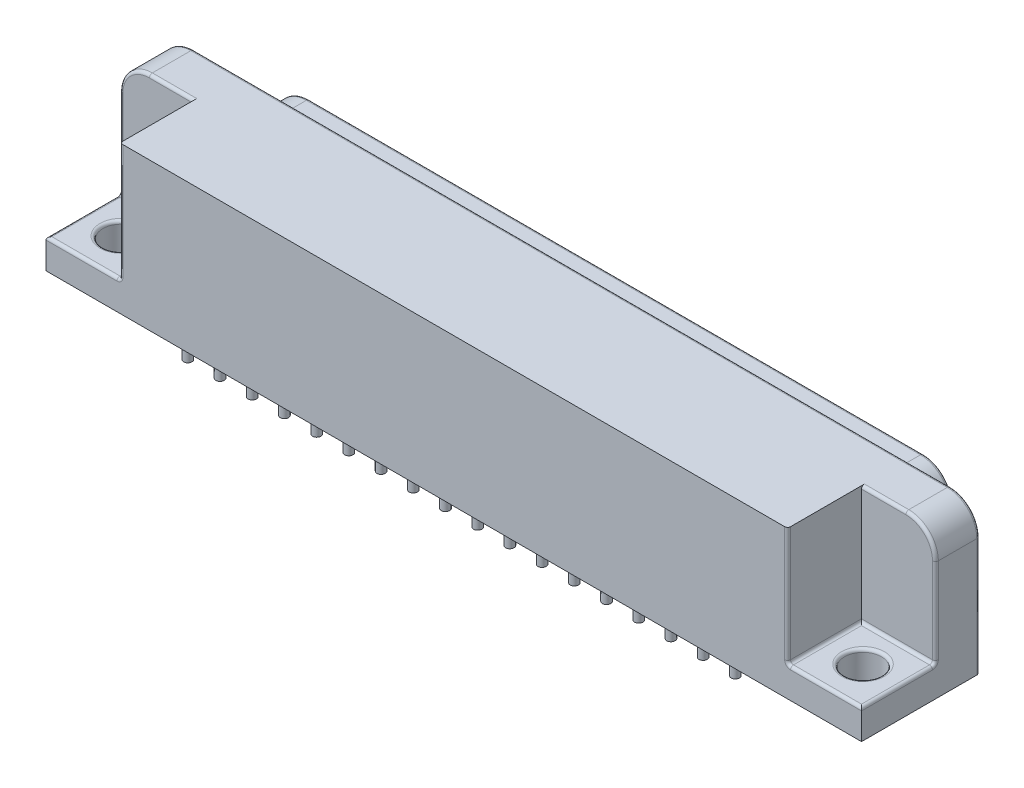
SolidWorks part; units mm, degrees
ref_plane "Front Plane" through (0, 0, 0) normal (0, 0, 1) x (1, 0, 0)
ref_plane "Top Plane" through (0, 0, 0) normal (0, 1, 0) x (1, 0, 0)
ref_plane "Right Plane" through (0, 0, 0) normal (1, 0, 0) x (0, 0, -1)
sketch "Sketch1" plane through (0, 0, 0) normal (0, 1, 0) x (1, 0, 0)
  line L1 (-10.16, -2.032) -> (59.944, -2.032)
  line L2 (-10.16, -2.032) -> (-10.16, 8.128)
  line L3 (-10.16, 8.128) -> (59.944, 8.128)
  line L4 (59.944, -2.032) -> (59.944, 8.128)
  point P3 (24.892, 8.128)
  dimension "D1" = 70.104
  dimension "D2" = 10.16
  dimension "D3" = 2.032
  dimension "D4" = 10.16
extrude "Base-Extrude" add sketch "Sketch1" along normal blind 12.7
sketch "Sketch2" plane through (0, 0, -8.128) normal (0, 0, -1) x (-1, 0, 0)
  line L0 (-24.892, 12.7) -> (-24.892, -6.5379) construction
  line L1 (-59.944, 12.7) -> (10.16, 12.7) construction
  line L2 (-50.7446, 2.286) -> (0.9606, 2.286)
  line L3 (3.4543, 4.3435) -> (3.9949, 7.1375)
  line L4 (1.5011, 10.16) -> (-51.2851, 10.16)
  line L6 (-53.2383, 4.3435) -> (-53.7789, 7.1375)
  line L7 (-59.944, 0) -> (10.16, 0) construction
  arc A0 (3.4543, 4.3435) -> (0.9606, 2.286) centre (0.9606, 4.826) cw
  arc A1 (1.5011, 10.16) -> (3.9949, 7.1375) centre (1.5011, 7.62) cw
  arc A2 (-51.2851, 10.16) -> (-53.7789, 7.1375) centre (-51.2851, 7.62) ccw
  arc A3 (-53.2383, 4.3435) -> (-50.7446, 2.286) centre (-50.7446, 4.826) ccw
  point P4 (-24.892, 10.16)
  point P12 (3.0563, 2.286)
  point P21 (-24.892, 2.286)
  dimension "D5" = 2.54
  dimension "D1" = 2.286
  dimension "D2" = 2.54
  dimension "D3" = 100.95
  dimension "D4" = 27.9483
extrude "Boss-Extrude1" add sketch "Sketch2" along normal blind 3.81
sketch "Sketch4" plane through (0, 0, -11.938) normal (0, 0, -1) x (-1, 0, 0)
  line L0 (10.16, 12.7) -> (10.16, 0) construction
  line L2 (-59.944, 12.7) -> (10.16, 12.7) construction
  circle A0 centre (0, 7.62) radius 0.635
  dimension "D1" = 1.27
  dimension "D2" = 10.16
  dimension "D3" = 5.08
extrude "Cut-Extrude1" cut sketch "Sketch4" against normal blind 5.08
sketch "Sketch5" plane through (0, 0, -11.938) normal (0, 0, -1) x (-1, 0, 0)
  line L0 (10.16, 12.7) -> (10.16, 0) construction
  line L2 (-59.944, 0) -> (10.16, 0) construction
  circle A0 centre (-1.397, 5.08) radius 0.635
  circle A1 centre (0, 7.62) radius 0.635 construction
  dimension "D2" = 5.08
  dimension "D1" = 11.557
extrude "Cut-Extrude2" cut sketch "Sketch5" against normal blind 5.08
sketch "Sketch6" plane through (0, 0, 0) normal (0, -1, 0) x (1, 0, 0)
  circle A0 centre (0, 0) radius 0.3556
  dimension "D1" = 0.7112
extrude "Boss-Extrude2" add sketch "Sketch6" along normal blind 2.54
pattern_linear "LPattern1" count 19 spacing 2.7686 along (1, 0, 0) skipping (18, 0) of "Boss-Extrude2"
pattern_linear "LPattern2" count 19 spacing 2.7686 along (1, 0, 0) of "Cut-Extrude1"
pattern_linear "LPattern3" count 18 spacing 2.7686 along (1, 0, 0) of "Cut-Extrude2"
sketch "Sketch7" plane through (0, 0, 0) normal (0, -1, 0) x (1, 0, 0)
  line L1 (-10.16, -8.128) -> (-10.16, 2.032) construction
  circle A0 centre (1.397, -2.54) radius 0.3556
  dimension "D1" = 0.7112
  dimension "D2" = 11.557
  dimension "D3" = 2.54
extrude "Boss-Extrude3" add sketch "Sketch7" along normal up to surface (2.54 mm away) up to face at (0, -2.54, -0.3556)
pattern_linear "LPattern4" count 17 spacing 2.7686 along (1, 0, 0) of "Boss-Extrude3"
ref_plane "Centreline Plane" through (24.892, 0, 0) normal (1, 0, 0) x (0, 0, -1)
sketch "Sketch9" plane through (0, 0, 2.032) normal (0, 0, 1) x (1, 0, 0)
  line L1 (-10.16, 12.7) -> (-3.8049, 12.7)
  line L2 (-10.16, 12.7) -> (-10.16, 2.54)
  line L3 (-10.16, 2.54) -> (-3.8049, 2.54)
  line L4 (-3.8049, 12.7) -> (-3.8049, 2.54)
  dimension "D1" = 10.16
  dimension "D2" = 6.3551
extrude "Cut-Extrude3" cut sketch "Sketch9" against normal blind 6.35
sketch "Sketch11" plane through (0, 2.54, 0) normal (0, 1, 0) x (-1, 0, 0)
  line L0 (10.16, 2.032) -> (3.8049, 2.032) construction
  line L1 (10.16, -4.318) -> (10.16, 2.032) construction
  circle A0 centre (6.985, -1.27) radius 1.5875
  point P2 (6.9825, 2.032)
  dimension "D1" = 3.175
  dimension "D2" = 3.302
  dimension "D3" = 3.175
extrude "Cut-Extrude4" cut sketch "Sketch11" against normal through all
mirror "Mirror1" about plane through (24.892, 0, 0) normal (1, 0, 0) of "Cut-Extrude4", "Cut-Extrude3"
fillet "Fillet1" radius 2.54 2 edges at (-10.16, 12.7, -6.223) (59.944, 7.62, -4.318)
fillet "Fillet2" radius 0.254 68 edges at (7.6708, 7.62, -11.938) (10.4394, 7.62, -11.938) (13.208, 7.62, -11.938) (15.9766, 7.62, -11.938) (18.7452, 7.62, -11.938) (21.5138, 7.62, -11.938) (24.2824, 7.62, -11.938) (27.051, 7.62, -11.938) (29.8196, 7.62, -11.938) (32.5882, 7.62, -11.938) (35.3568, 7.62, -11.938) (38.1254, 7.62, -11.938) (40.894, 7.62, -11.938) (43.6626, 7.62, -11.938) (46.4312, 7.62, -11.938) (49.1998, 7.62, -11.938) (3.5306, 5.08, -11.938) (6.2992, 5.08, -11.938) (9.0678, 5.08, -11.938) (11.8364, 5.08, -11.938) (14.605, 5.08, -11.938) (17.3736, 5.08, -11.938) (20.1422, 5.08, -11.938) (22.9108, 5.08, -11.938) (25.6794, 5.08, -11.938) (28.448, 5.08, -11.938) (31.2166, 5.08, -11.938) (33.9852, 5.08, -11.938) (36.7538, 5.08, -11.938) (39.5224, 5.08, -11.938) (-2.5771, 2.8668, -11.938) (42.291, 5.08, -11.938) (-3.7246, 5.7405, -11.938) (45.0596, 5.08, -11.938) (-3.4604, 9.2365, -11.938) (47.8282, 5.08, -11.938) (24.892, 10.16, -11.938) (53.2444, 9.2365, -11.938) (53.5086, 5.7405, -11.938) (52.3611, 2.8668, -11.938) (24.892, 2.286, -11.938) (-10.16, 2.54, -1.143) (-5.7125, 12.7, -4.318) (-6.9825, 2.54, -4.318) (-3.8049, 2.54, -1.143) (-6.9825, 2.54, 2.032) (-3.8049, 7.62, 2.032) (-6.985, 2.54, 0.3175) (56.7665, 2.54, 2.032) (59.944, 2.54, -1.143) (53.5889, 7.62, 2.032) (53.5889, 2.54, -1.143) (56.7665, 2.54, -4.318) (55.4965, 12.7, -4.318) (56.769, 2.54, 0.3175) (24.892, 12.7, -8.128) (-10.16, 6.35, -4.318) (-9.4161, 11.9561, -4.318) (-10.16, 5.08, -8.128) (59.944, 5.08, -8.128) (59.2001, 11.9561, -8.128) (-9.4161, 11.9561, -8.128) (59.944, 6.35, -4.318) (59.2001, 11.9561, -4.318) (-0.635, 7.62, -11.938) (0.762, 5.08, -11.938) (2.1336, 7.62, -11.938) (4.9022, 7.62, -11.938)
sketch "Component_Outline" plane through (0, 0, 0) normal (0, -1, 0) x (1, 0, 0)
  line L0 (50.7446, -11.938) -> (-0.9606, -11.938) construction
  line L1 (-10.16, 2.032) -> (59.944, 2.032)
  line L2 (-10.16, 2.032) -> (-10.16, -11.938)
  line L3 (-10.16, -11.938) -> (59.944, -11.938)
  line L4 (59.944, 2.032) -> (59.944, -11.938)
  line L5 (59.944, 2.032) -> (59.944, -7.874) construction
